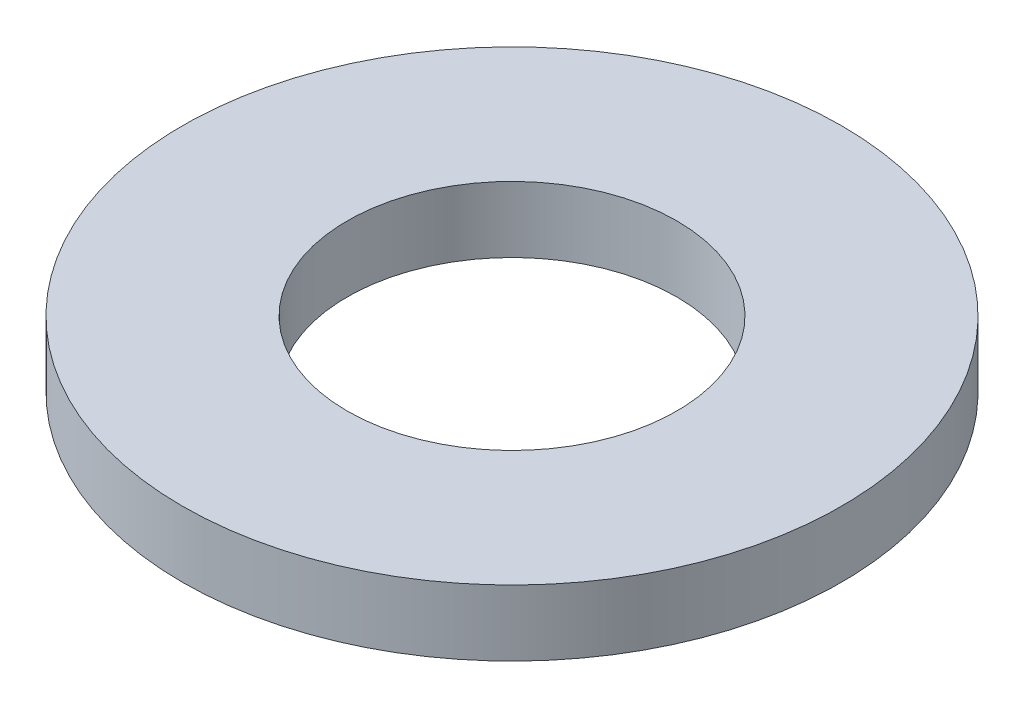
SolidWorks part; units mm, degrees
ref_plane "Front" through (0, 0, 0) normal (0, 0, 1) x (1, 0, 0)
ref_plane "Top" through (0, 0, 0) normal (0, 1, 0) x (1, 0, 0)
ref_plane "Right" through (0, 0, 0) normal (1, 0, 0) x (0, 0, -1)
sketch "Sketch1" plane through (0, 0, 0) normal (0, 1, 0) x (1, 0, 0)
  circle A0 centre (0, 0) radius 2.5
  circle A1 centre (0, 0) radius 5
  dimension "D1" = 5
  dimension "D2" = 10
extrude "Boss-Extrude1" add sketch "Sketch1" along normal blind 1
